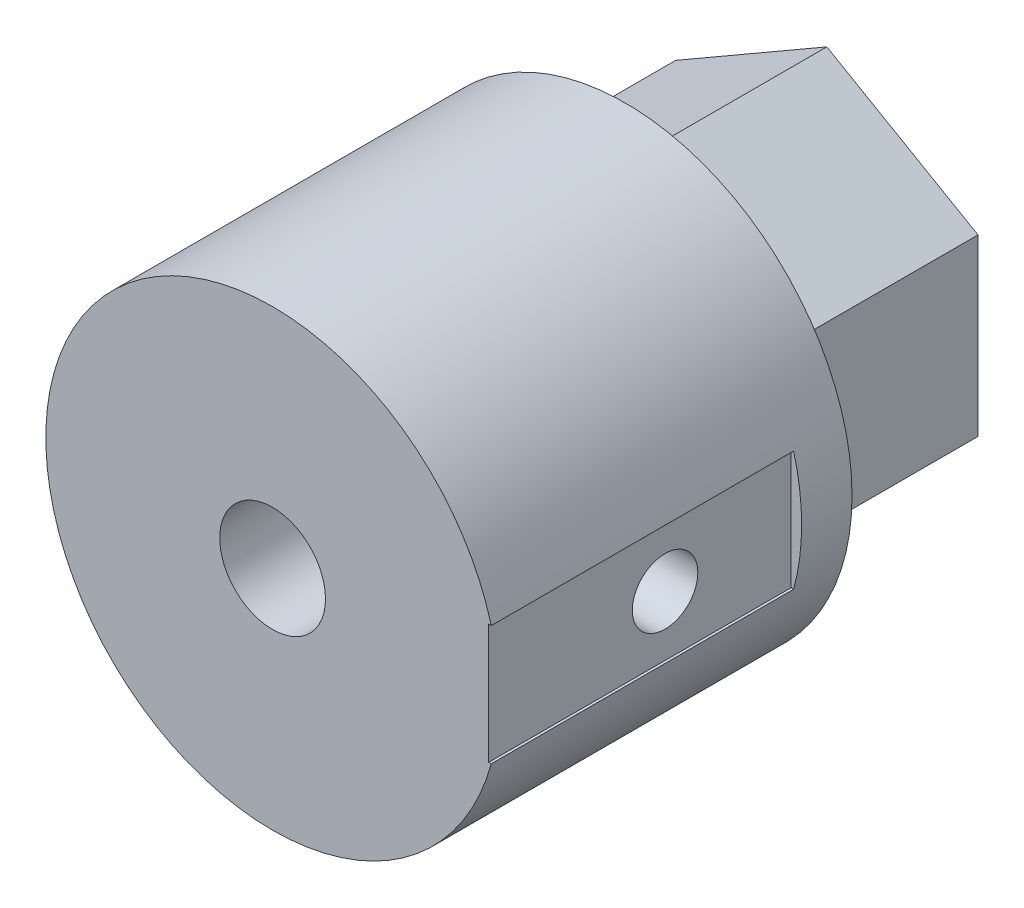
SolidWorks part; units mm, degrees
ref_plane "Plan de face" through (0, 0, 0) normal (0, 0, 1) x (1, 0, 0)
ref_plane "Plan de dessus" through (0, 0, 0) normal (0, 1, 0) x (1, 0, 0)
ref_plane "Plan de droite" through (0, 0, 0) normal (1, 0, 0) x (0, 0, -1)
sketch "Esquisse1" plane through (0, 0, 0) normal (0, 0, 1) x (1, 0, 0)
  line L1 (6, 3.4641) -> (0, 6.9282)
  line L2 (0, 6.9282) -> (-6, 3.4641)
  line L3 (-6, 3.4641) -> (-6, -3.4641)
  line L4 (-6, -3.4641) -> (0, -6.9282)
  line L5 (0, -6.9282) -> (6, -3.4641)
  line L6 (6, -3.4641) -> (6, 3.4641)
  circle A0 centre (0, 0) radius 6 construction
extrude "Boss.-Extru.1" add sketch "Esquisse1" along normal blind 22
sketch "Esquisse2" plane through (0, 0, 22) normal (0, 0, 1) x (1, 0, 0)
  circle A0 centre (0, 0) radius 1.7
extrude "Enlèv. mat.-Extru.1" cut sketch "Esquisse2" against normal blind 23
sketch "Esquisse3" plane through (0, 0, 22) normal (0, 0, 1) x (1, 0, 0)
  circle A0 centre (0, 0) radius 1.3
  circle A1 centre (0, 0) radius 9
extrude "Boss.-Extru.2" add sketch "Esquisse3" against normal blind 14
sketch "Esquisse4" plane through (0, 0, 22) normal (0, 0, 1) x (1, 0, 0)
  line L0 (9, 0) -> (-9, 0) construction
  line L2 (8.5787, -2.3757) -> (9.4213, -2.3757)
  line L3 (8.5787, -2.3757) -> (8.5787, 2.3757)
  line L4 (8.5787, 2.3757) -> (9.4213, 2.3757)
  line L5 (9.4213, -2.3757) -> (9.4213, 2.3757)
  line L6 (8.5787, -2.3757) -> (9.4213, 2.3757) construction
  line L7 (8.5787, 2.3757) -> (9.4213, -2.3757) construction
  circle A0 centre (0, 0) radius 9 construction
extrude "Enlèv. mat.-Extru.2" cut sketch "Esquisse4" against normal blind 12
sketch "Esquisse5" plane through (8.5787, 0, 0) normal (1, 0, 0) x (0, 0, -1)
  line L0 (-22, 0) -> (-8, 0) construction
  line L1 (-22, 2.3757) -> (-22, -2.3757) construction
  line L2 (-8, 2.7214) -> (-8, -2.7214) construction
  circle A0 centre (-15, 0) radius 1.3
extrude "Enlèv. mat.-Extru.3" cut sketch "Esquisse5" against normal blind 27
sketch "Esquisse6" plane through (0, 0, 22) normal (0, 0, 1) x (1, 0, 0)
  circle A0 centre (0, 0) radius 2.1
extrude "Enlèv. mat.-Extru.4" cut sketch "Esquisse6" against normal blind 14
